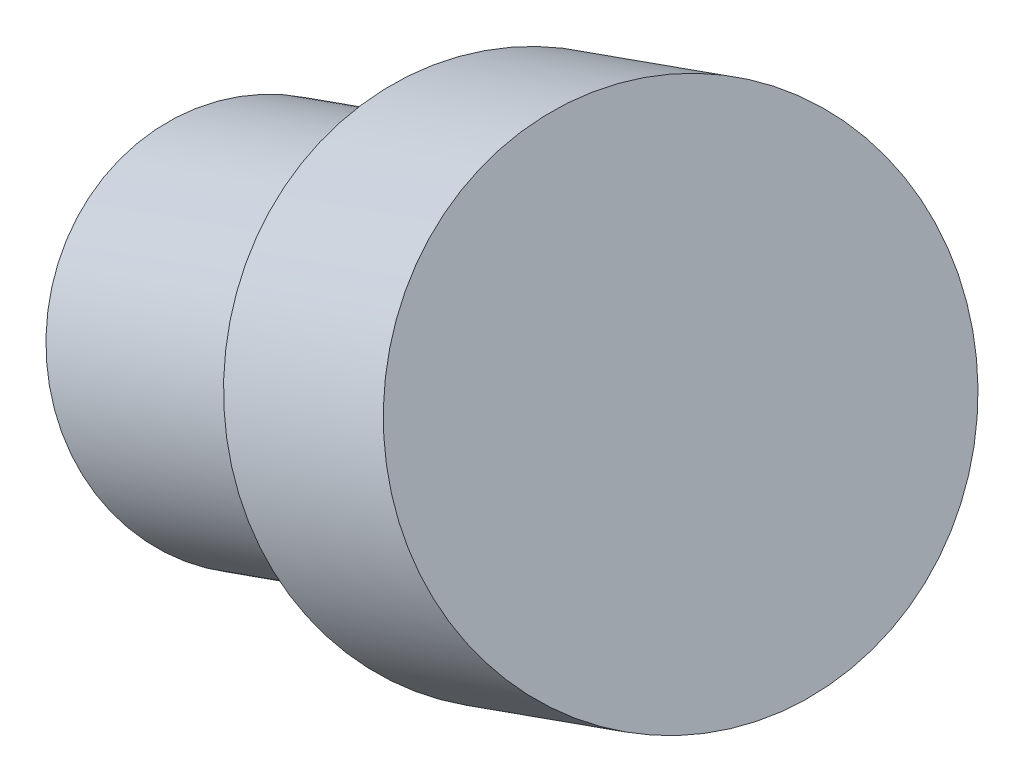
SolidWorks part; units mm, degrees
ref_plane "Front Plane" through (0, 0, 0) normal (0, 0, 1) x (1, 0, 0)
ref_plane "Top Plane" through (0, 0, 0) normal (0, 1, 0) x (1, 0, 0)
ref_plane "Right Plane" through (0, 0, 0) normal (1, 0, 0) x (0, 0, -1)
sketch "Sketch2" plane through (0, 0, 0) normal (0, 1, 0) x (1, 0, 0)
  circle A0 centre (0, 0) radius 32.1849
extrude "Boss-Extrude1" add sketch "Sketch2" along normal blind 78 contours A0
sketch "Sketch3" plane through (0, 78, 0) normal (0, 1, 0) x (1, 0, 0)
  circle A0 centre (0, 0) radius 44.4528
extrude "Boss-Extrude2" add sketch "Sketch3" along normal blind 48
move or copy body "Body-Move/Copy1" bodies to move or copy 102 copy no translate (-72.9607, 52.2188, 0)
move or copy body "Body-Move/Copy2" bodies to move or copy 103 copy no rotation origin (-95.5514, 86.9316, 17.3344) rotation axis (0.5628, 0.7048, -0.4319) rotation angle 94.867
sketch3d "3DSketch1"
  circle A1 centre (135.0493, -52.5149, 50.7637) radius 39.1604
  point P0 (135.0493, -52.5149, 50.7637)
  point P3 (0, 0, 0)
  point P6 (135.0493, -13.3545, 50.7637)
